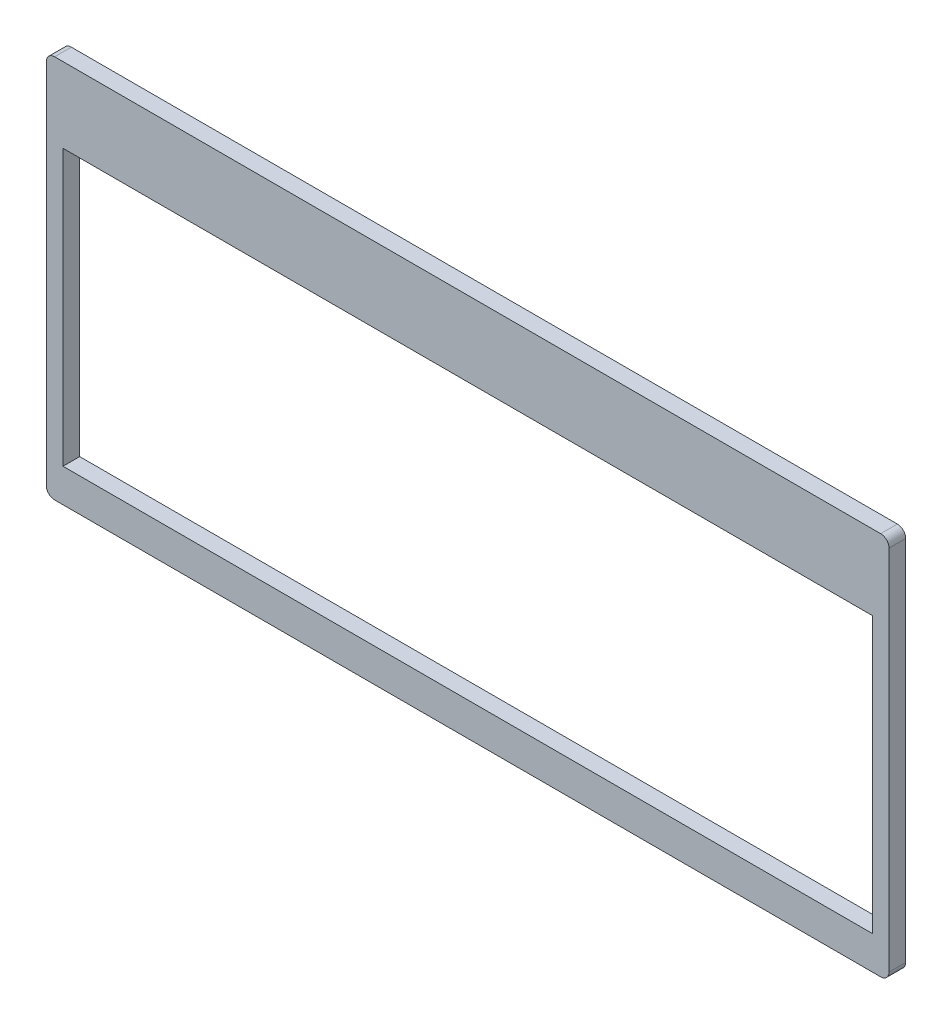
SolidWorks part; units mm, degrees
ref_plane "前视基准面" through (0, 0, 0) normal (0, 0, 1) x (1, 0, 0)
ref_plane "上视基准面" through (0, 0, 0) normal (0, 1, 0) x (1, 0, 0)
ref_plane "右视基准面" through (0, 0, 0) normal (1, 0, 0) x (0, 0, -1)
sketch "草图1" plane through (0, 0, 0) normal (0, 0, 1) x (1, 0, 0)
  line L1 (-50.5, 23) -> (50.5, 23)
  line L2 (-50.5, 23) -> (-50.5, -23)
  line L3 (-50.5, -23) -> (50.5, -23)
  line L4 (50.5, 23) -> (50.5, -23)
  line L5 (-50.5, 23) -> (50.5, -23) construction
  line L6 (-50.5, -23) -> (50.5, 23) construction
  line L7 (-48.5, 14) -> (48.5, 14)
  line L8 (-48.5, 14) -> (-48.5, -19)
  line L9 (-48.5, -19) -> (48.5, -19)
  line L10 (48.5, 14) -> (48.5, -19)
  line L11 (-48.5, 14) -> (48.5, -19) construction
  line L12 (-48.5, -19) -> (48.5, 14) construction
  point P0 (0, 0)
  point P6 (0, -2.5)
  dimension "D1" = 101
  dimension "D2" = 46
  dimension "D3" = 9
  dimension "D4" = 4
  dimension "D5" = 2
  dimension "D6" = 2
extrude "凸台-拉伸1" add sketch "草图1" along normal blind 2
fillet "圆角1" radius 1 1 edges at (-50.5, 23, 1)
fillet "圆角2" radius 1 3 edges at (50.5, -23, 1) (50.5, 23, 1) (-50.5, -23, 1)
